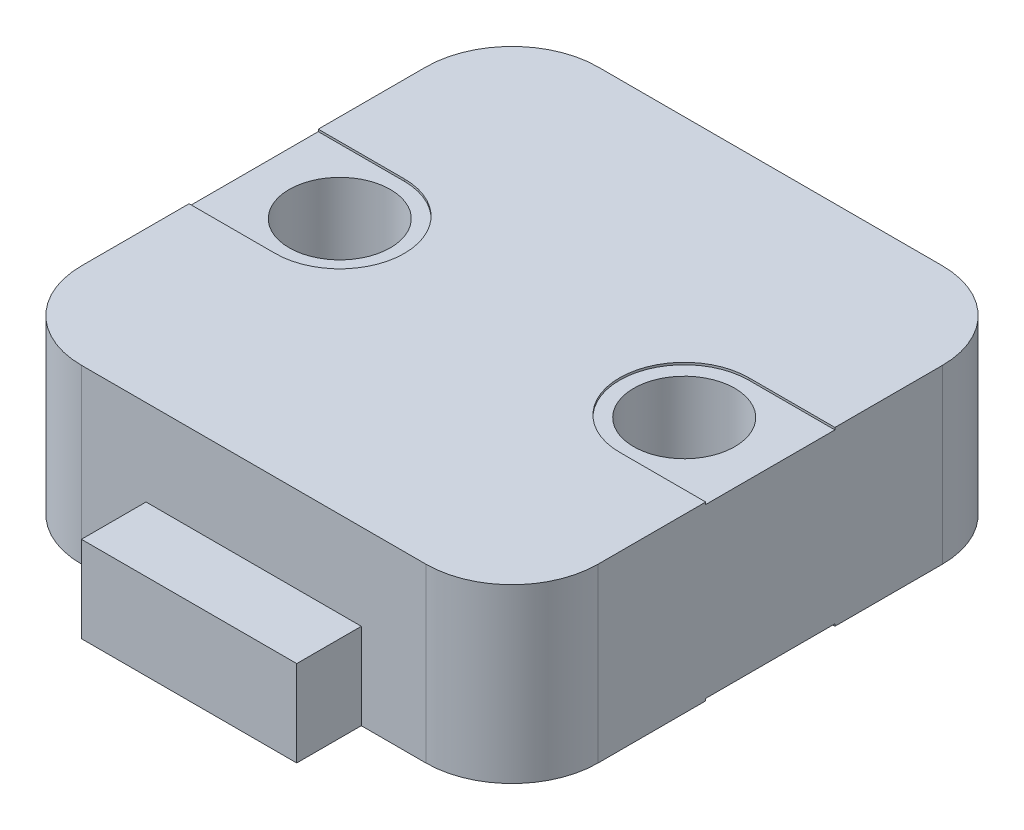
SolidWorks part; units mm, degrees
ref_plane "Alzado" through (0, 0, 0) normal (0, 0, 1) x (1, 0, 0)
ref_plane "Planta" through (0, 0, 0) normal (0, 1, 0) x (1, 0, 0)
ref_plane "Vista lateral" through (0, 0, 0) normal (1, 0, 0) x (0, 0, -1)
sketch "Croquis1" plane through (0, 0, 0) normal (0, 1, 0) x (1, 0, 0)
  line L0 (-8, 0) -> (8, 0) construction
  line L1 (-8, 12) -> (8, 12)
  line L2 (-12, 8) -> (-12, -8)
  line L3 (-8, -12) -> (8, -12)
  line L4 (12, 8) -> (12, -8)
  line L5 (-12, 12) -> (12, -12) construction
  line L6 (-12, -12) -> (12, 12) construction
  line L7 (0, 0) -> (0, 3.2159) construction
  arc A0 (-12, -8) -> (-8, -12) centre (-8, -8) ccw
  arc A1 (8, -12) -> (12, -8) centre (8, -8) ccw
  arc A2 (8, 12) -> (12, 8) centre (8, 8) cw
  arc A3 (-8, 12) -> (-12, 8) centre (-8, 8) ccw
  circle A4 centre (-8, 0) radius 2.35
  circle A5 centre (8, 0) radius 2.35
  point P0 (0, 0)
  dimension "D3" = 4
  dimension "D5" = 4.7
  dimension "D1" = 24
  dimension "D2" = 24
  dimension "D4" = 16
extrude "Saliente-Extruir1" add sketch "Croquis1" along normal mid plane 8
sketch "Croquis2" plane through (0, 0, 0) normal (0, 1, 0) x (1, 0, 0)
  line L0 (-8, -12) -> (8, -12) construction
  line L1 (-8, -12) -> (8, -12) construction
  line L6 (5, -15) -> (-5, -15)
  line L7 (5, -15) -> (5, -9)
  line L8 (5, -9) -> (-5, -9)
  line L9 (-5, -15) -> (-5, -9)
  line L10 (5, -15) -> (-5, -9) construction
  line L11 (5, -9) -> (-5, -15) construction
  point P2 (0, -12)
  point P7 (0, 0)
  dimension "D1" = 10
  dimension "D2" = 6
extrude "Saliente-Extruir2" add sketch "Croquis2" along normal blind 4 from surface at -4 starting at face at (0, -4, 0)
sketch "Croquis3" plane through (0, 4, 0) normal (0, 1, 0) x (1, 0, 0)
  line L0 (0, 0) -> (0, 3.8364) construction
  line L1 (-8, 3) -> (-16.5304, 3)
  line L2 (-16.5304, 3) -> (-16.5304, -3)
  line L3 (-16.5304, -3) -> (-8, -3)
  line L4 (16.5304, -3) -> (8, -3)
  line L5 (16.5304, 3) -> (16.5304, -3)
  line L6 (8, 3) -> (16.5304, 3)
  circle A0 centre (8, 0) radius 2.35 construction
  circle A1 centre (-8, 0) radius 2.35 construction
  circle A2 centre (8, 0) radius 2.35 construction
  circle A3 centre (-8, 0) radius 2.35 construction
  arc A4 (-8, -3) -> (-8, 3) centre (-8, 0) ccw
  arc A5 (8, -3) -> (8, 3) centre (8, 0) cw
  dimension "D1" = 6
extrude "Cortar-Extruir1" cut sketch "Croquis3" against normal blind 0.1
mirror "Simetría1" about plane through (0, 0, 0) normal (0, 1, 0) of "Cortar-Extruir1"
